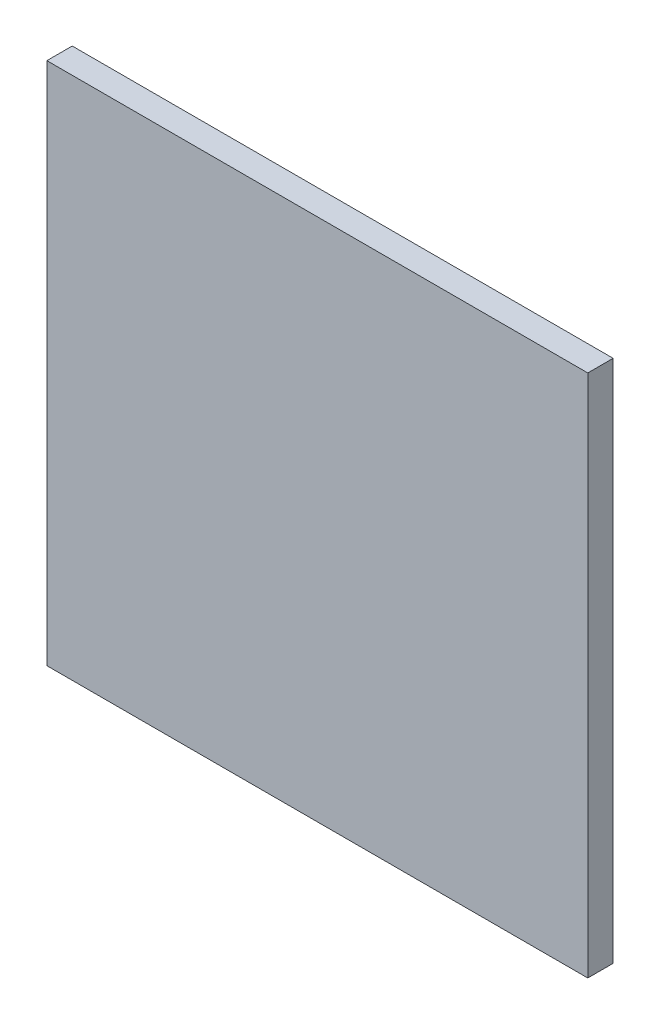
SolidWorks part; units mm, degrees
ref_plane "Plan de face" through (0, 0, 0) normal (0, 0, 1) x (1, 0, 0)
ref_plane "Plan de dessus" through (0, 0, 0) normal (0, 1, 0) x (1, 0, 0)
ref_plane "Plan de droite" through (0, 0, 0) normal (1, 0, 0) x (0, 0, -1)
sketch "Esquisse1" plane through (0, 0, 0) normal (0, 0, 1) x (1, 0, 0)
  line L0 (0, 15.5) -> (0, 0) construction
  line L1 (-16, 15.5) -> (16, 15.5)
  line L2 (-16, 15.5) -> (-16, -15.5)
  line L3 (-16, -15.5) -> (16, -15.5)
  line L4 (16, 15.5) -> (16, -15.5)
  line L5 (16, 0) -> (0, 0) construction
  dimension "D1" = 32
  dimension "D2" = 31
extrude "Boss.-Extru.1" add sketch "Esquisse1" along normal mid plane 1.5
